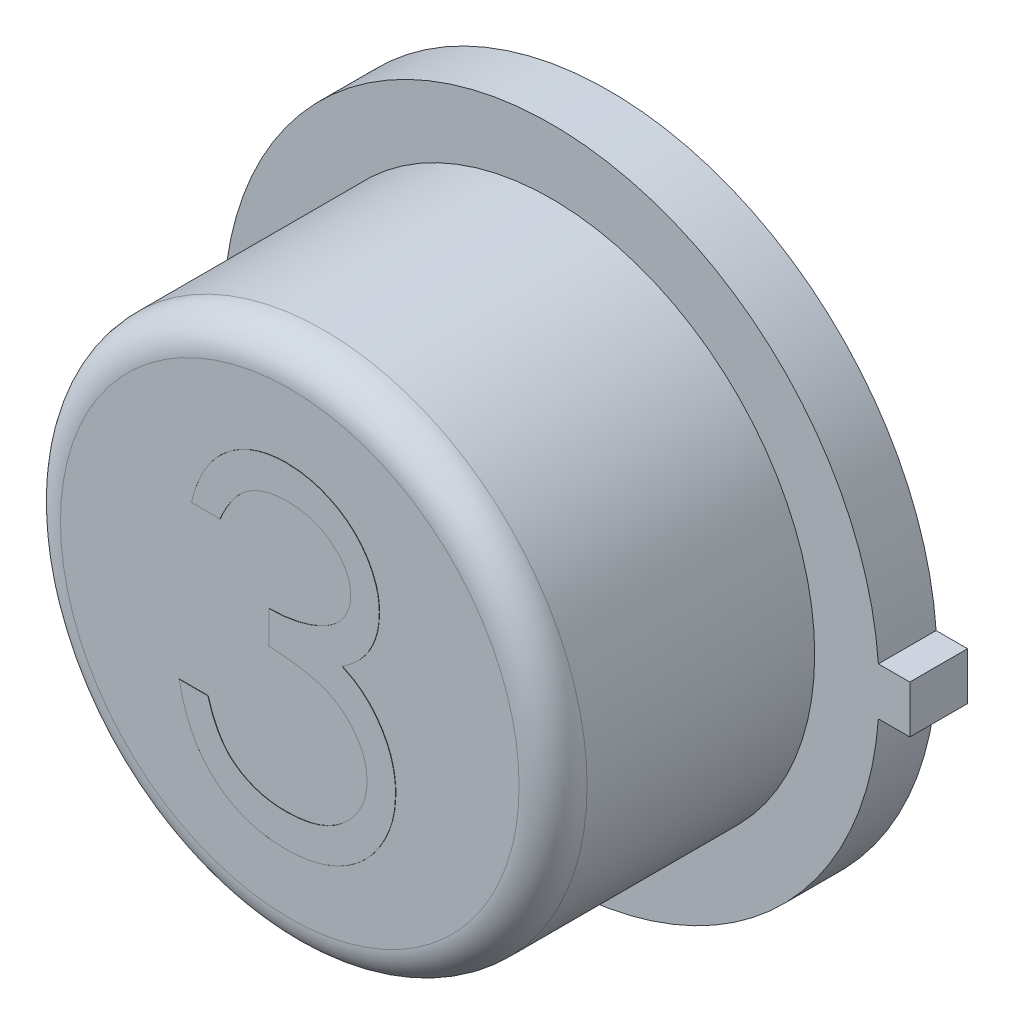
SolidWorks part; units mm, degrees
ref_plane "Front Plane" through (0, 0, 0) normal (0, 0, 1) x (1, 0, 0)
ref_plane "Top Plane" through (0, 0, 0) normal (0, 1, 0) x (1, 0, 0)
ref_plane "Right Plane" through (0, 0, 0) normal (1, 0, 0) x (0, 0, -1)
sketch "Sketch1" plane through (0, 0, 0) normal (0, 0, 1) x (1, 0, 0)
  line L1 (2.4511, 0.1778) -> (2.6797, 0.1778)
  line L3 (2.4511, -0.1778) -> (2.6797, -0.1778)
  line L4 (2.6797, 0.1778) -> (2.6797, -0.1778)
  line L5 (2.4511, 0.1778) -> (2.4444, 0.1778)
  line L6 (2.4511, -0.1778) -> (2.4446, -0.1778)
  arc A0 (2.4446, 0.1778) -> (2.4446, -0.1778) centre (0, 0) ccw
  dimension "D1" = 4.9022
  dimension "D2" = 0.3556
  dimension "D3" = 0.2286
extrude "Boss-Extrude1" add sketch "Sketch1" along normal blind 0.4318
sketch "Sketch2" plane through (0, 0, 0.4318) normal (0, 0, 1) x (1, 0, 0)
  circle A0 centre (0, 0) radius 1.9685
  dimension "D1" = 3.937
extrude "Boss-Extrude2" add sketch "Sketch2" along normal blind 1.9558
sketch "Sketch3" plane through (0, 0, 0) normal (0, 0, -1) x (-1, 0, 0)
  circle A0 centre (0, 0) radius 1.7576
extrude "Boss-Extrude3" add sketch "Sketch3" along normal blind 0.0025
fillet "Fillet1" radius 0.254 1 edges at (1.9685, 0, 2.3876)
sketch "Sketch4" plane through (0, 0, 2.3876) normal (0, 0, 1) x (1, 0, 0)
  line L0 (-1.2065, -1.2181) -> (1.2065, -1.2181) construction
  circle A0 centre (0, 0) radius 1.7145 construction
  text T0 "3" font "Century Gothic" height in points 9
  dimension "D1" = 2.413
extrude "Boss-Extrude6" add sketch "Sketch4" along normal blind 0.0025
